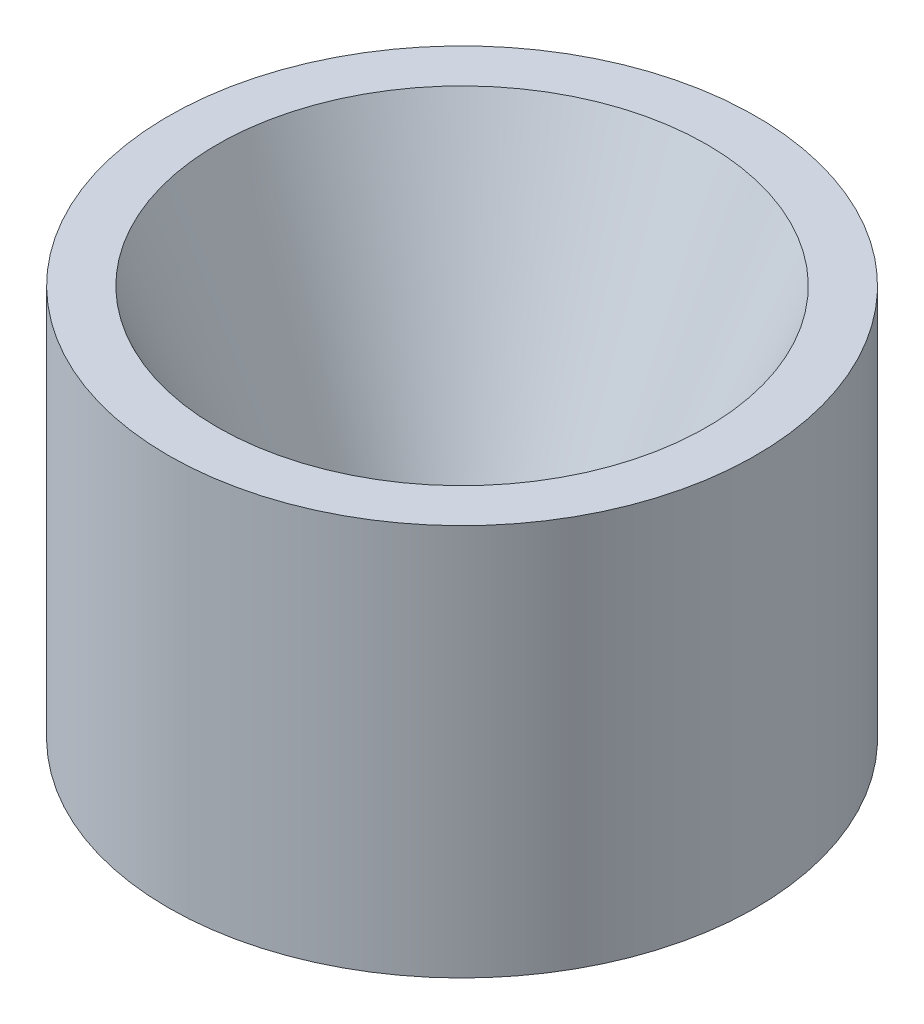
SolidWorks part; units mm, degrees
ref_plane "Alzado" through (0, 0, 0) normal (0, 0, 1) x (1, 0, 0)
ref_plane "Planta" through (0, 0, 0) normal (0, 1, 0) x (1, 0, 0)
ref_plane "Vista lateral" through (0, 0, 0) normal (1, 0, 0) x (0, 0, -1)
sketch "Croquis1" plane through (0, 0, 0) normal (0, 0, 1) x (1, 0, 0)
  line L0 (0, 6.8864) -> (0, -4.6364) construction
  line L1 (1.3, 2.8745) -> (3, 2.8745)
  line L2 (3, 2.8745) -> (3, 6.8745)
  line L3 (3, 6.8745) -> (2.5, 6.8745)
  line L4 (1, 3.3745) -> (1, 3.2874)
  line L5 (2.5, 6.8745) -> (1, 3.3745)
  line L6 (1, 3.2874) -> (1.3, 2.8745)
  point P3 (1, 2.8745)
  point P7 (1, 6.8745)
  dimension "D1" = 3
  dimension "D2" = 1
  dimension "D3" = 4
  dimension "D4" = 0.5
  dimension "D5" = 0.5
  dimension "D6" = 0.3
  dimension "D7" = 54
revolve "Revolución2" add sketch "Croquis1" angle 360 about L0
